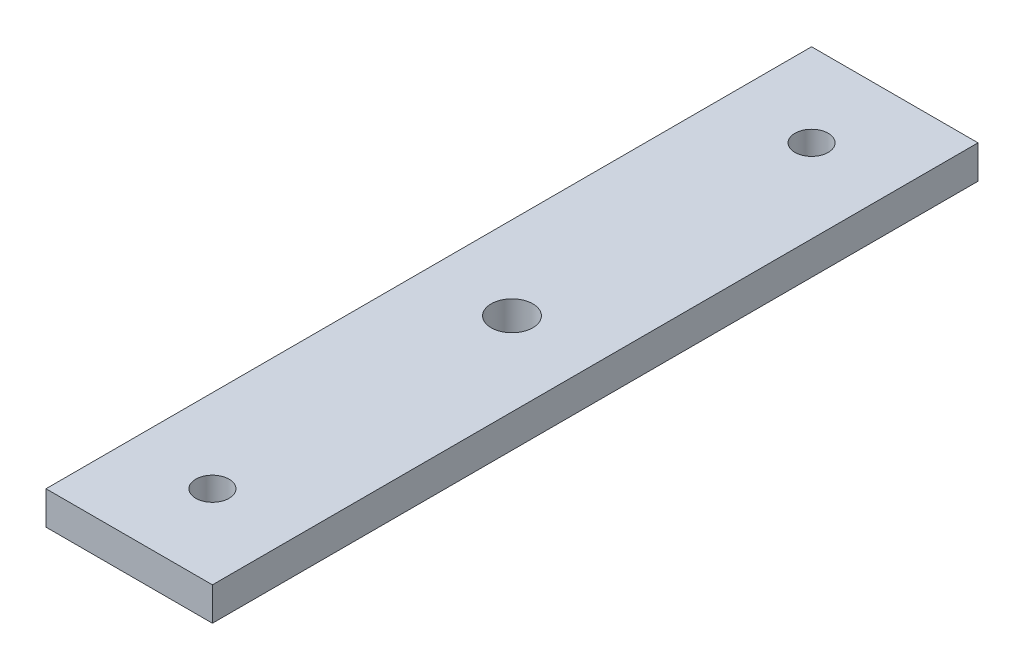
SolidWorks part; units mm, degrees
ref_plane "Front Plane" through (0, 0, 0) normal (0, 0, 1) x (1, 0, 0)
ref_plane "Top Plane" through (0, 0, 0) normal (0, 1, 0) x (1, 0, 0)
ref_plane "Right Plane" through (0, 0, 0) normal (1, 0, 0) x (0, 0, -1)
sketch "Sketch1" plane through (0, 0, 0) normal (0, 1, 0) x (1, 0, 0)
  line L1 (-50, 230) -> (50, 230)
  line L2 (-50, 230) -> (-50, -230)
  line L3 (-50, -230) -> (50, -230)
  line L4 (50, 230) -> (50, -230)
  line L5 (-50, 230) -> (50, -230) construction
  line L6 (-50, -230) -> (50, 230) construction
  circle A0 centre (0, -180) radius 10
  circle A1 centre (0, 180) radius 10
  point P0 (0, 0)
  dimension "D3" = 20
  dimension "D4" = 20
  dimension "D6" = 50
  dimension "D1" = 100
  dimension "D2" = 460
  dimension "D5" = 50
extrude "Boss-Extrude1" add sketch "Sketch1" along normal blind 20
sketch "Sketch2" plane through (0, 20, 0) normal (0, 1, 0) x (1, 0, 0)
  circle A0 centre (0, 0) radius 12.5
  dimension "D1" = 25
extrude "Cut-Extrude1" cut sketch "Sketch2" against normal through all
